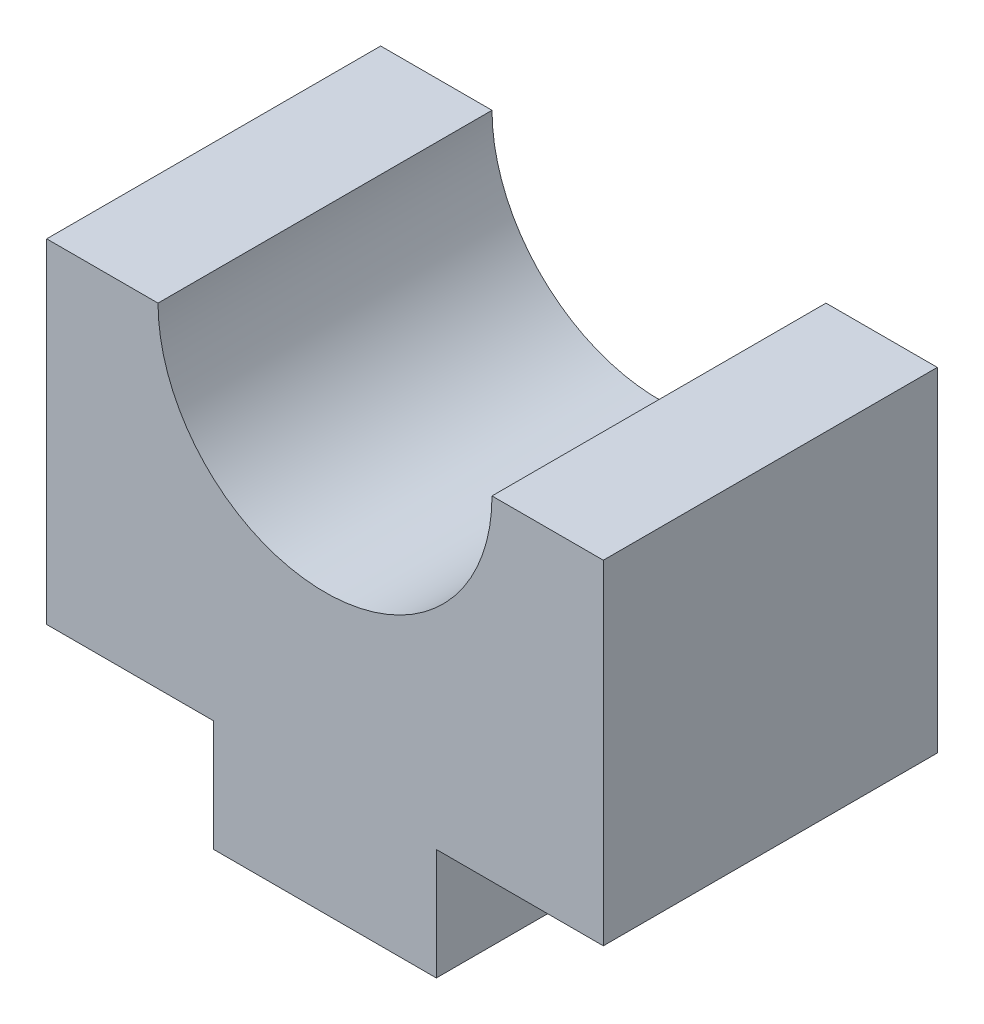
SolidWorks part; units mm, degrees
ref_plane "Alzado" through (0, 0, 0) normal (0, 0, 1) x (1, 0, 0)
ref_plane "Planta" through (0, 0, 0) normal (0, 1, 0) x (1, 0, 0)
ref_plane "Vista lateral" through (0, 0, 0) normal (1, 0, 0) x (0, 0, -1)
sketch "Croquis1" plane through (0, 0, 0) normal (0, 0, 1) x (1, 0, 0)
  line L0 (0, 0) -> (10, 0)
  line L1 (10, 0) -> (10, 5)
  line L2 (10, 5) -> (17.5, 5)
  line L3 (17.5, 5) -> (17.5, 20)
  line L4 (17.5, 20) -> (12.5, 20)
  line L5 (0, 0) -> (0, 5)
  line L6 (0, 5) -> (-7.5, 5)
  line L7 (-7.5, 5) -> (-7.5, 20)
  line L8 (-7.5, 20) -> (-2.5, 20)
  arc A0 (-2.5, 20) -> (12.5, 20) centre (5, 20) ccw
  point P12 (18.4896, 5)
  point P13 (0, 0)
  point P14 (5, 0)
  point P15 (5, 20)
  point P16 (5, 20)
  dimension "D6" = 7.5
  dimension "D1" = 10
  dimension "D2" = 5
  dimension "D3" = 7.5
  dimension "D4" = 15
  dimension "D5" = 5
extrude "Saliente-Extruir1" add sketch "Croquis1" against normal blind 15
